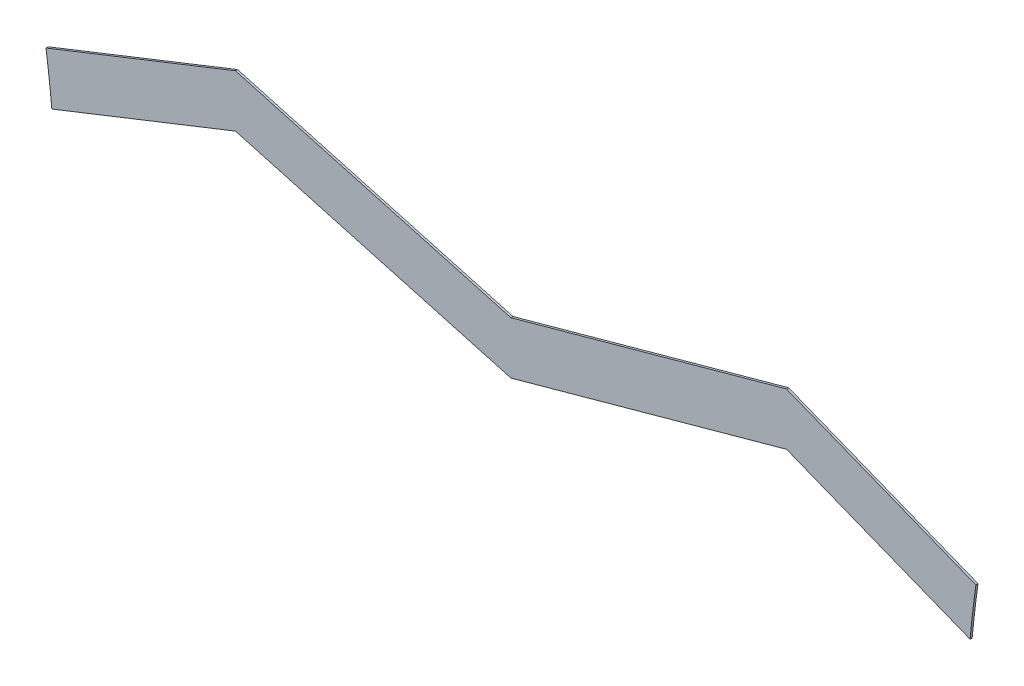
SolidWorks part; units mm, degrees
ref_plane "Alzado" through (0, 0, 0) normal (0, 0, 1) x (1, 0, 0)
ref_plane "Planta" through (0, 0, 0) normal (0, 1, 0) x (1, 0, 0)
ref_plane "Vista lateral" through (0, 0, 0) normal (1, 0, 0) x (0, 0, -1)
sketch "Model" plane through (0, 0, 0) normal (0, 0, 1) x (1, 0, 0)
  line L0 (59.8216, 14.578) -> (60.2727, 14.3994)
  line L1 (16.0808, 16.7898) -> (25.1404, 20.3758)
  line L2 (25.1404, 20.3758) -> (38.3161, 16.7362)
  line L3 (38.3161, 16.7362) -> (51.492, 20.3754)
  line L4 (51.492, 20.3754) -> (60.5515, 16.789)
  line L5 (59.8216, 14.578) -> (51.492, 17.8754)
  line L6 (51.492, 17.8754) -> (38.3161, 14.2362)
  line L7 (16.807, 14.5772) -> (25.1403, 17.8758)
  line L8 (25.1403, 17.8758) -> (38.3161, 14.2362)
  line L9 (16.3595, 14.4001) -> (16.807, 14.5772)
  arc A0 (60.5515, 16.789) -> (60.2727, 14.3994) centre (113.0574, 9.4528) ccw
  arc A1 (16.3595, 14.4001) -> (16.0808, 16.7898) centre (-36.4253, 9.4553) ccw
extrude "Saliente-Extruir1" add sketch "Model" along normal blind 0.1
